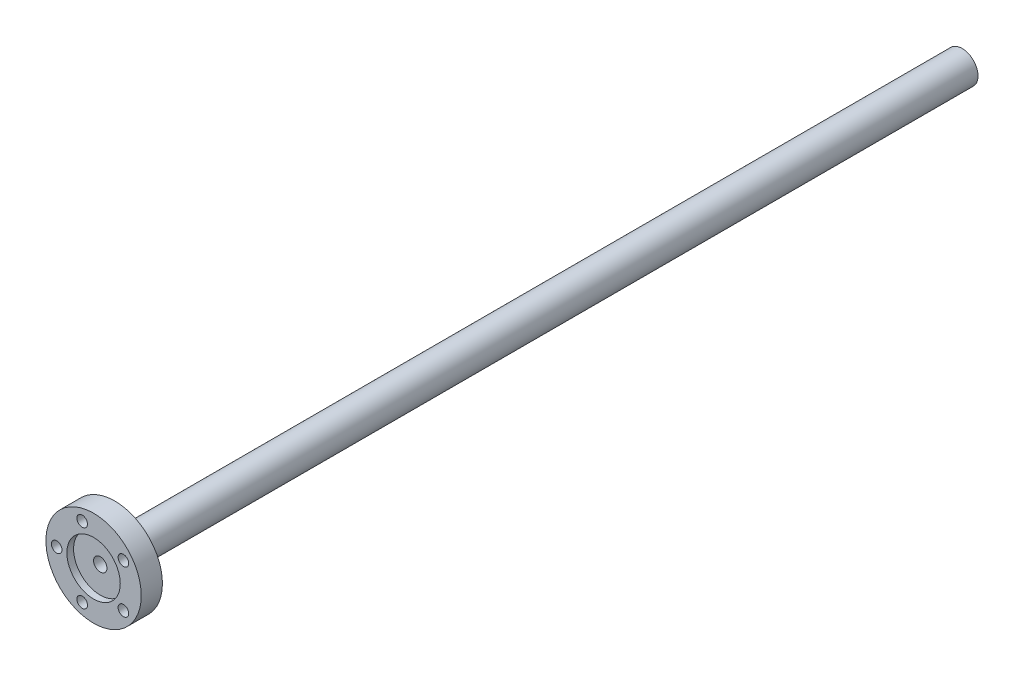
SolidWorks part; units mm, degrees
ref_plane "Front Plane" through (0, 0, 0) normal (0, 0, 1) x (1, 0, 0)
ref_plane "Top Plane" through (0, 0, 0) normal (0, 1, 0) x (1, 0, 0)
ref_plane "Right Plane" through (0, 0, 0) normal (1, 0, 0) x (0, 0, -1)
sketch "Sketch1" plane through (0, 0, 0) normal (0, 1, 0) x (1, 0, 0)
  line L0 (14.2875, 6.35) -> (0, 6.35)
  line L1 (0, 6.35) -> (0, 0)
  line L2 (0, 0) -> (14.2875, 0)
  line L3 (14.2875, 0) -> (14.2875, 6.35)
  line L4 (0, 6.35) -> (0, 0) construction
revolve "Revolve1" add sketch "Sketch1" angle 360 about L4
sketch "Sketch2" plane through (0, 0, -6.35) normal (0, 0, -1) x (-1, 0, 0)
  circle A0 centre (0, 0) radius 4.7625
  circle A1 centre (0, 0) radius 14.2875 construction
  dimension "D1" = 9.525
extrude "Boss-Extrude1" add sketch "Sketch2" along normal blind 254
sketch "Sketch3" plane through (0, 0, -260.35) normal (0, 0, -1) x (-1, 0, 0)
  line L0 (1, -4.6563) -> (1, -3.7833)
  line L1 (1, -3.7833) -> (-1, -3.7833)
  line L2 (-1, -3.7833) -> (-1, -4.6563)
  line L3 (0, -1000) -> (0, 49000) construction
  circle A0 centre (0, 0) radius 4.7625 construction
  arc A2 (-1, -4.6563) -> (1, -4.6563) centre (0, 0) ccw
  point P6 (0, 0)
  dimension "D1" = 0.873
  dimension "D2" = 2
extrude "Cut-Extrude1" cut sketch "Sketch3" against normal blind 32.004
ref_plane "Plane1" through (0, 0, 0) normal (0, -1, 0) x (1, 0, 0)
sketch "Sketch4" plane through (0, 0, 0) normal (0, -1, 0) x (1, 0, 0)
  line L0 (-9.4725, 0) -> (-11.06, 0)
  line L1 (-11.06, 0) -> (-11.06, -6.35)
  line L2 (-11.06, -6.35) -> (-9.5233, -6.35)
  line L3 (-9.5233, -6.35) -> (-9.5233, -4.7625)
  line L4 (-9.5233, -4.7625) -> (-9.4725, -4.7625)
  line L5 (-9.4725, -4.7625) -> (-9.4725, 0)
  line L6 (-11.06, 0) -> (-11.06, -6.35) construction
revolve "Cut-Revolve1" cut sketch "Sketch4" angle 360 about L6
hole_wizard "Hole1" positions "Sketch6" profile "Sketch5" legacy
sketch "Sketch6" plane through (0, 0, 0) normal (0, 0, 1) x (1, 0, 0)
  point P0 (-3.4177, -10.5187)
sketch "Sketch5" plane through (-3.4177, -10.5187, 0) normal (1, 0, 0) x (0, -1, 0)
  line L0 (0, 0) -> (0, 260.35)
  line L1 (0, 260.35) -> (1.0922, 260.35)
  line L2 (1.0922, 260.35) -> (1.0922, 4.7625)
  line L3 (1.0922, 4.7625) -> (1.5875, 4.7625)
  line L4 (1.5875, 4.7625) -> (1.5875, 0)
  line L5 (1.5875, 0) -> (0, 0)
  line L6 (0, 110) -> (0, -10) construction
  dimension "Diameter" = 2.1844
  dimension "Depth" = 260.35
  dimension "C-Bore Diameter" = 3.175
  dimension "C-Bore Depth" = 4.7625
hole_wizard "Hole2" positions "Sketch8" profile "Sketch7" legacy
sketch "Sketch8" plane through (0, 0, 0) normal (0, 0, 1) x (1, 0, 0)
  point P0 (8.9477, -6.5009)
sketch "Sketch7" plane through (8.9477, -6.5009, 0) normal (1, 0, 0) x (0, -1, 0)
  line L0 (0, 0) -> (0, 260.35)
  line L1 (0, 260.35) -> (1.0922, 260.35)
  line L2 (1.0922, 260.35) -> (1.0922, 4.7625)
  line L3 (1.0922, 4.7625) -> (1.5875, 4.7625)
  line L4 (1.5875, 4.7625) -> (1.5875, 0)
  line L5 (1.5875, 0) -> (0, 0)
  line L6 (0, 110) -> (0, -10) construction
  dimension "Diameter" = 2.1844
  dimension "Depth" = 260.35
  dimension "C-Bore Diameter" = 3.175
  dimension "C-Bore Depth" = 4.7625
hole_wizard "Hole3" positions "Sketch10" profile "Sketch9" legacy
sketch "Sketch10" plane through (0, 0, 0) normal (0, 0, 1) x (1, 0, 0)
  point P0 (8.9477, 6.5009)
sketch "Sketch9" plane through (8.9477, 6.5009, 0) normal (1, 0, 0) x (0, -1, 0)
  line L0 (0, 0) -> (0, 260.35)
  line L1 (0, 260.35) -> (1.0922, 260.35)
  line L2 (1.0922, 260.35) -> (1.0922, 4.7625)
  line L3 (1.0922, 4.7625) -> (1.5875, 4.7625)
  line L4 (1.5875, 4.7625) -> (1.5875, 0)
  line L5 (1.5875, 0) -> (0, 0)
  line L6 (0, 110) -> (0, -10) construction
  dimension "Diameter" = 2.1844
  dimension "Depth" = 260.35
  dimension "C-Bore Diameter" = 3.175
  dimension "C-Bore Depth" = 4.7625
hole_wizard "Hole4" positions "Sketch12" profile "Sketch11" legacy
sketch "Sketch12" plane through (0, 0, 0) normal (0, 0, 1) x (1, 0, 0)
  point P0 (-3.4177, 10.5187)
sketch "Sketch11" plane through (-3.4177, 10.5187, 0) normal (1, 0, 0) x (0, -1, 0)
  line L0 (0, 0) -> (0, 260.35)
  line L1 (0, 260.35) -> (1.0922, 260.35)
  line L2 (1.0922, 260.35) -> (1.0922, 4.7625)
  line L3 (1.0922, 4.7625) -> (1.5875, 4.7625)
  line L4 (1.5875, 4.7625) -> (1.5875, 0)
  line L5 (1.5875, 0) -> (0, 0)
  line L6 (0, 110) -> (0, -10) construction
  dimension "Diameter" = 2.1844
  dimension "Depth" = 260.35
  dimension "C-Bore Diameter" = 3.175
  dimension "C-Bore Depth" = 4.7625
hole_wizard "Hole5" positions "Sketch14" profile "Sketch13" legacy
sketch "Sketch14" plane through (0, 0, 0) normal (0, 0, 1) x (1, 0, 0)
  point P0 (0, 0)
sketch "Sketch13" plane through (0, 0, 0) normal (1, 0, 0) x (0, -1, 0)
  line L0 (0, 0) -> (0, 5)
  line L1 (0, 5) -> (2, 5)
  line L2 (2, 5) -> (2, 2)
  line L3 (2, 2) -> (8, 2)
  line L4 (8, 2) -> (8, 0)
  line L5 (8, 0) -> (0, 0)
  line L6 (0, 110) -> (0, -10) construction
  dimension "Diameter" = 4
  dimension "Depth" = 5
  dimension "C-Bore Diameter" = 16
  dimension "C-Bore Depth" = 2
fillet "Fillet1" radius 0.7874 1 edges at (-4.7625, 0, -6.35)
